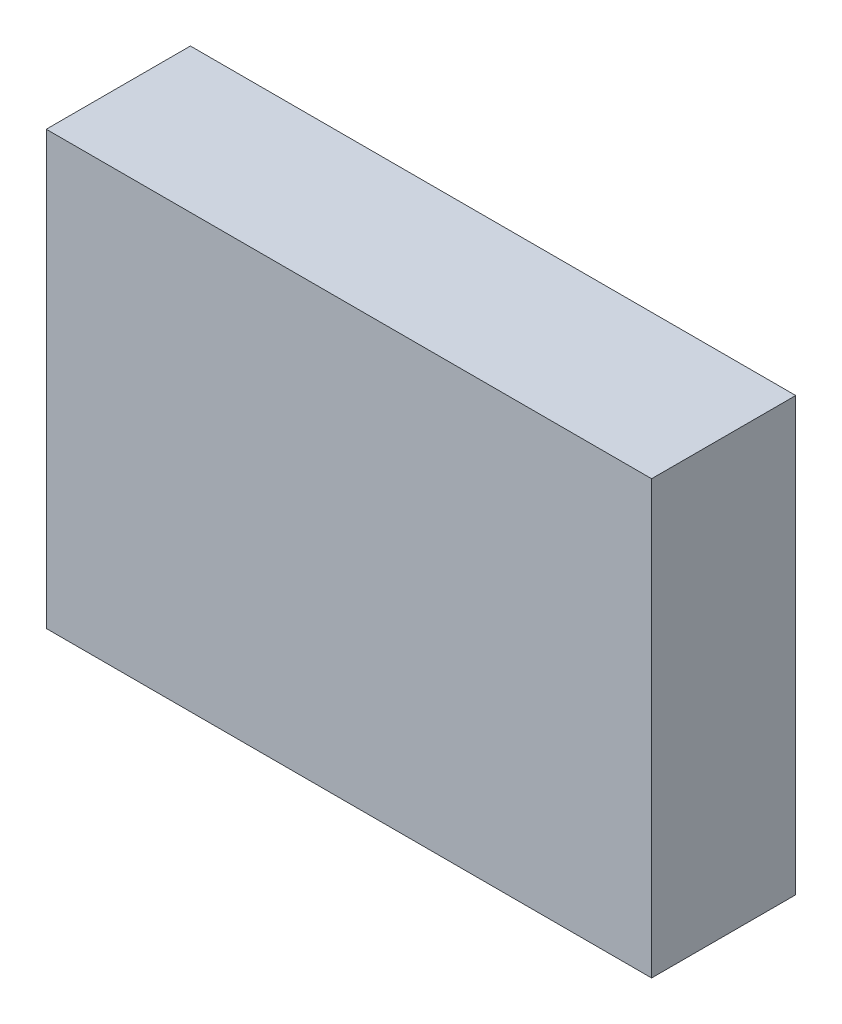
SolidWorks part; units mm, degrees
ref_plane "Front Plane" through (0, 0, 0) normal (0, 0, 1) x (1, 0, 0)
ref_plane "Top Plane" through (0, 0, 0) normal (0, 1, 0) x (1, 0, 0)
ref_plane "Right Plane" through (0, 0, 0) normal (1, 0, 0) x (0, 0, -1)
sketch "Sketch1" plane through (0, 0, 0) normal (0, 0, 1) x (1, 0, 0)
  line L1 (-34.764, 35.1705) -> (49.236, 35.1705)
  line L2 (-34.764, 35.1705) -> (-34.764, -24.8295)
  line L3 (-34.764, -24.8295) -> (49.236, -24.8295)
  line L4 (49.236, 35.1705) -> (49.236, -24.8295)
  dimension "D1" = 84
  dimension "D2" = 60
extrude "Boss-Extrude1" add sketch "Sketch1" along normal blind 20
